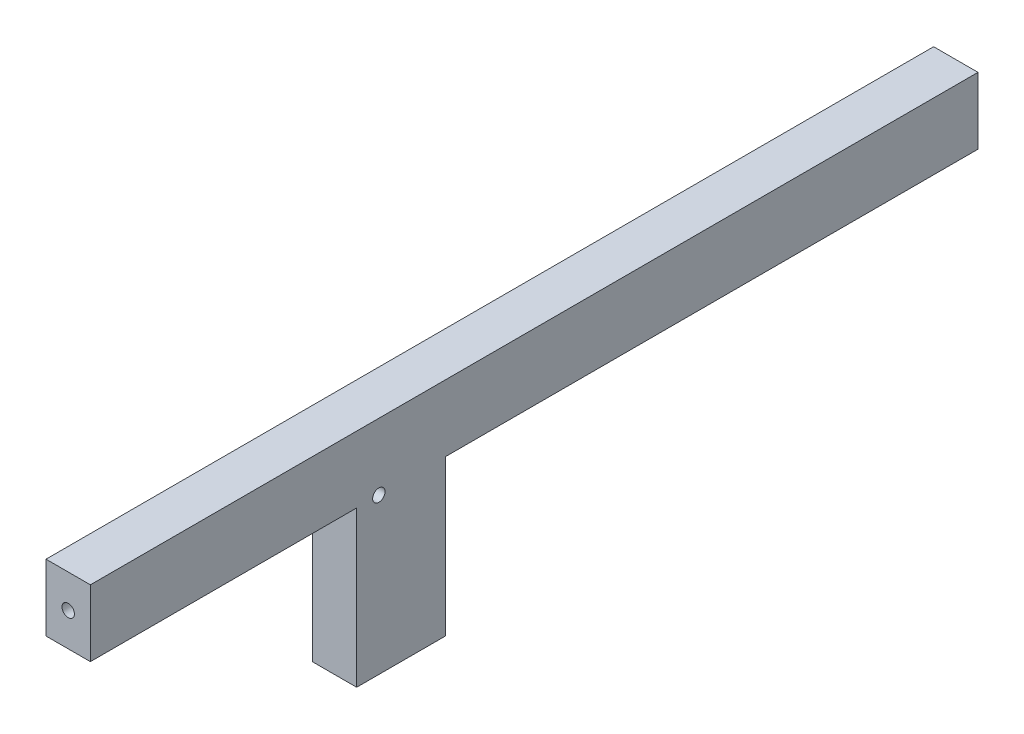
SolidWorks part; units mm, degrees
ref_plane "Front Plane" through (0, 0, 0) normal (0, 0, 1) x (1, 0, 0)
ref_plane "Top Plane" through (0, 0, 0) normal (0, 1, 0) x (1, 0, 0)
ref_plane "Right Plane" through (0, 0, 0) normal (1, 0, 0) x (0, 0, -1)
sketch "Sketch1" plane through (0, 0, 0) normal (1, 0, 0) x (0, 0, -1)
  line L0 (-6.35, -6.8928) -> (-44.45, -6.8928)
  line L1 (82.55, -6.8928) -> (6.35, -6.8928)
  line L2 (82.55, -6.8928) -> (82.55, 2.6322)
  line L3 (82.55, 2.6322) -> (-44.45, 2.6322)
  line L4 (-44.45, -6.8928) -> (-44.45, 2.6322)
  line L5 (0, -29.1178) -> (0, 0) construction
  line L6 (-44.45, -3.7178) -> (82.55, -3.7178) construction
  line L7 (6.35, -29.1178) -> (-6.35, -29.1178)
  line L8 (6.35, -29.1178) -> (6.35, -6.8928)
  line L10 (-6.35, -29.1178) -> (-6.35, -6.8928)
  dimension "D1" = 44.45
  dimension "D2" = 82.55
  dimension "D3" = 9.525
  dimension "D4" = 6.35
  dimension "D5" = 12.7
  dimension "D6" = 31.75
extrude "Boss-Extrude1" add sketch "Sketch1" along normal mid plane 6.35
sketch "Sketch2" plane through (0, 0, -6.35) normal (0, 0, -1) x (-1, 0, 0)
  line L0 (3.175, -29.1178) -> (3.175, -6.8928) construction
  line L1 (-1.5875, -9.4853) -> (0, -9.4853)
  line L2 (-1.5875, -9.4853) -> (-1.5875, -12.6603)
  line L3 (-1.5875, -12.6603) -> (0, -12.6603)
  line L4 (0, -9.4853) -> (0, -12.6603)
  line L5 (-1.5875, -9.4853) -> (0, -12.6603) construction
  line L6 (-1.5875, -12.6603) -> (0, -9.4853) construction
  line L7 (-1.5875, -22.1853) -> (0, -22.1853)
  line L8 (-1.5875, -22.1853) -> (-1.5875, -25.3603)
  line L9 (-1.5875, -25.3603) -> (0, -25.3603)
  line L10 (0, -22.1853) -> (0, -25.3603)
  line L11 (-1.5875, -22.1853) -> (0, -25.3603) construction
  line L12 (-1.5875, -25.3603) -> (0, -22.1853) construction
  point P0 (-0.7937, -11.0728)
  point P5 (-0.7938, -23.7728)
  dimension "D1" = 3.175
  dimension "D2" = 1.5875
  dimension "D3" = 3.175
  dimension "D4" = 9.525
extrude "Cut-Extrude1" cut sketch "Sketch2" against normal blind 3.175
hole_wizard "#2-56 Tapped Hole1" positions "Sketch6" profile "Sketch5" tap size "#2-56" standard "Ansi Inch"
sketch "Sketch6" plane through (3.175, 0, 0) normal (1, 0, 0) x (0, 0, -1)
  point P0 (-3.175, -6.8928)
sketch "Sketch5" plane through (3.175, -6.8928, 3.175) normal (0, 1, 0) x (0, 0, -1)
  line L0 (0, 0) -> (0, 6.1222)
  line L1 (0, 6.1222) -> (0.889, 5.588)
  line L2 (0.889, 5.588) -> (0.889, 0)
  line L5 (0.889, 0) -> (0, 0)
  line L10 (0, 6.1222) -> (-0.889, 5.588) construction
  line L11 (0, -6.35) -> (0, 107.95) construction
  dimension "Tap Drill Dia." = 1.778
  dimension "Tap Drill Depth" = 5.588
  dimension "Drill Angle" = 118
cosmetic thread "Hole Thread1" parameters "D1"=4.318, "D2"=2.1844
hole_wizard "#2-56 Tapped Hole2" positions "Sketch8" profile "Sketch7" tap size "#2-56" standard "Ansi Inch"
sketch "Sketch8" plane through (0, 0, 44.45) normal (0, 0, 1) x (1, 0, 0)
  point P0 (0, -2.1303)
sketch "Sketch7" plane through (0, -2.1303, 44.45) normal (1, 0, 0) x (0, -1, 0)
  line L0 (0, 0) -> (0, 11.2022)
  line L1 (0, 11.2022) -> (0.889, 10.668)
  line L2 (0.889, 10.668) -> (0.889, 0)
  line L5 (0.889, 0) -> (0, 0)
  line L10 (0, 11.2022) -> (-0.889, 10.668) construction
  line L11 (0, -6.35) -> (0, 107.95) construction
  dimension "Tap Drill Dia." = 1.778
  dimension "Tap Drill Depth" = 10.668
  dimension "Drill Angle" = 118
cosmetic thread "Hole Thread2" parameters "D1"=4.318, "D2"=2.1844
hole_wizard "#2-56 Tapped Hole3" positions "Sketch10" profile "Sketch9" tap size "#2-56" standard "Ansi Inch"
sketch "Sketch10" plane through (0, 0, -82.55) normal (0, 0, -1) x (-1, 0, 0)
  point P0 (0, -2.1303)
sketch "Sketch9" plane through (0, -2.1303, -82.55) normal (1, 0, 0) x (0, 1, 0)
  line L0 (0, 0) -> (0, 11.2022)
  line L1 (0, 11.2022) -> (0.889, 10.668)
  line L2 (0.889, 10.668) -> (0.889, 0)
  line L5 (0.889, 0) -> (0, 0)
  line L10 (0, 11.2022) -> (-0.889, 10.668) construction
  line L11 (0, -6.35) -> (0, 107.95) construction
  dimension "Tap Drill Dia." = 1.778
  dimension "Tap Drill Depth" = 10.668
  dimension "Drill Angle" = 118
cosmetic thread "Hole Thread3" parameters "D1"=4.318, "D2"=2.1844
